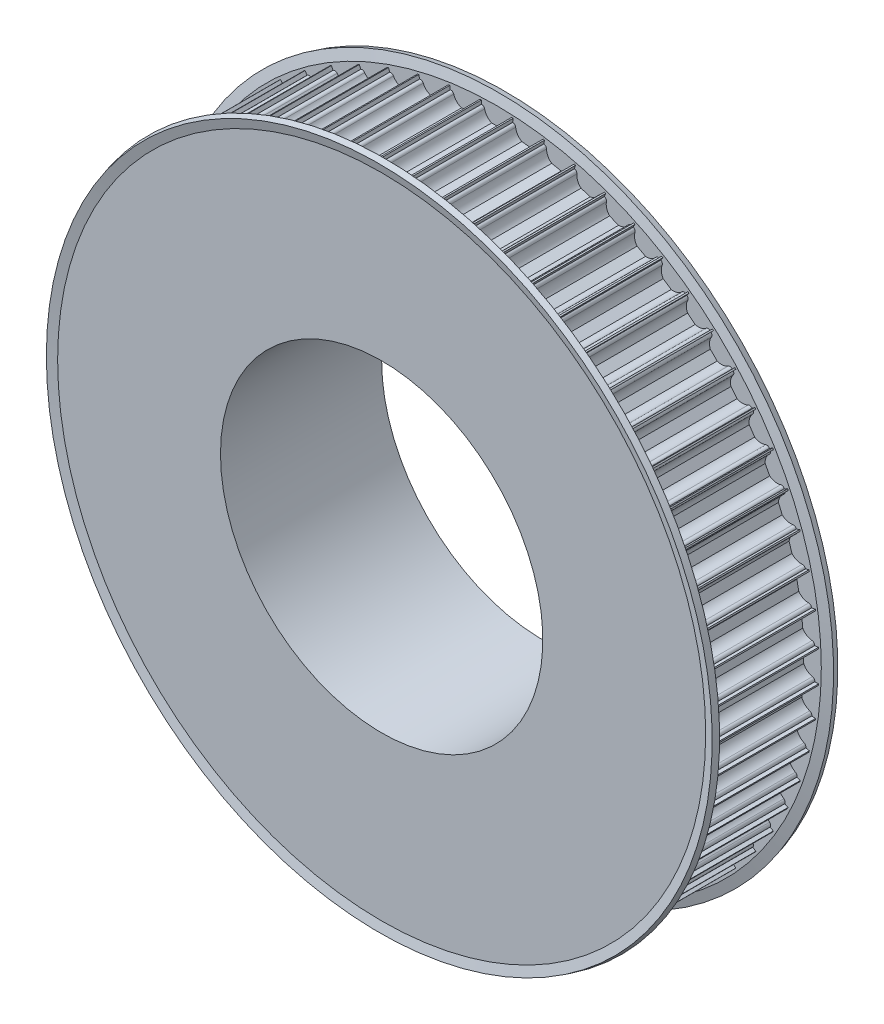
SolidWorks part; units mm, degrees
ref_plane "Front Plane" through (0, 0, 0) normal (0, 0, 1) x (1, 0, 0)
ref_plane "Top Plane" through (0, 0, 0) normal (0, 1, 0) x (1, 0, 0)
ref_plane "Right Plane" through (0, 0, 0) normal (1, 0, 0) x (0, 0, -1)
ref_axis "Axis1" through (0, 0, -88.99) along (0, 0, 1)
sketch "Sketch1" plane through (0, 0, 0) normal (1, 0, 0) x (0, 0, -1)
  line L0 (0, 40) -> (0, 80)
  line L1 (0, 80) -> (30, 80)
  line L2 (30, 80) -> (30, 55.5)
  line L3 (30, 55.5) -> (40, 55.5)
  line L4 (40, 55.5) -> (40, 40)
  line L5 (40, 40) -> (0, 40)
  line L6 (88.99, 0) -> (-88.99, 0) construction
  dimension "D1" = 40
  dimension "D2" = 30
  dimension "D3" = 10
  dimension "D4" = 15.5
  dimension "D5" = 40
revolve "Revolve1" add sketch "Sketch1" angle 360 about axis through (0, 0, -88.99) along (0, 0, 1)
sketch "Sketch2" plane through (0, 0, 0) normal (0, 0, 1) x (1, 0, 0)
  line L0 (3.6742, 79) -> (3.75, 79)
  line L1 (-3.75, 81) -> (3.75, 81)
  line L2 (-3.75, 81) -> (-3.75, 79)
  line L3 (-3.75, 79) -> (-3.6742, 79)
  line L4 (3.75, 81) -> (3.75, 79)
  line L5 (-1.199, 76.25) -> (1.199, 76.25)
  arc A0 (-2.9394, 78.4) -> (-1.199, 76.25) centre (0, 79) ccw
  arc A1 (-2.9394, 78.4) -> (-3.6742, 79) centre (-3.6742, 78.25) ccw
  arc A2 (2.9394, 78.4) -> (3.6742, 79) centre (3.6742, 78.25) cw
  arc A3 (1.199, 76.25) -> (2.9394, 78.4) centre (0, 79) ccw
  dimension "D1" = 3
  dimension "D5" = 0.75
  dimension "D6" = 0.75
  dimension "D2" = 2
  dimension "D3" = 7.5
  dimension "D4" = 79
  dimension "D7" = 2.75
extrude "Cut-Extrude1" cut sketch "Sketch2" against normal through all
pattern_circular "CirPattern1" count 64 over 360 about axis through (0, 0, 0) along (0, 0, 1) of "Cut-Extrude1"
sketch "Sketch4" plane through (0, 0, 0) normal (1, 0, 0) x (0, 0, -1)
  line L0 (0, -37.0014) -> (0, -39.5498) construction
  line L1 (0, 75.6121) -> (1.5, 75.6121)
  line L2 (0, 75.6121) -> (0, 80.6121)
  line L3 (0, 80.6121) -> (1.5, 80.6121) construction
  line L4 (1.5, 75.6121) -> (1.5, 80.6121)
  line L5 (1.5, 80.6121) -> (0.0511, 80.2238) construction
  line L6 (1.5, 80.6121) -> (0.8569, 83.0121)
  line L7 (0.0511, 80.2238) -> (-0.592, 82.6238)
  line L8 (0.8569, 83.0121) -> (-0.592, 82.6238)
  line L9 (15, -40.9775) -> (15, 34.3631) construction
  line L10 (30, -40.9775) -> (0, -40.9775) construction
  line L11 (30, 34.3631) -> (0, 34.3631) construction
  line L12 (29.1431, 83.0121) -> (30.592, 82.6238)
  line L13 (29.9489, 80.2238) -> (30.592, 82.6238)
  line L14 (28.5, 80.6121) -> (29.1431, 83.0121)
  line L15 (28.5, 80.6121) -> (29.9489, 80.2238) construction
  line L16 (28.5, 75.6121) -> (28.5, 80.6121)
  line L17 (30, 80.6121) -> (28.5, 80.6121) construction
  line L18 (30, 75.6121) -> (30, 80.6121)
  line L19 (30, 75.6121) -> (28.5, 75.6121)
  dimension "D1" = 1.5
  dimension "D2" = 5
  dimension "D3" = 1.5
  dimension "D4" = 165
  dimension "D5" = 2.4
  dimension "D6" = 0.7
revolve "Revolve2" add sketch "Sketch4" angle 360 about axis through (0, 0, -88.99) along (0, 0, 1)
